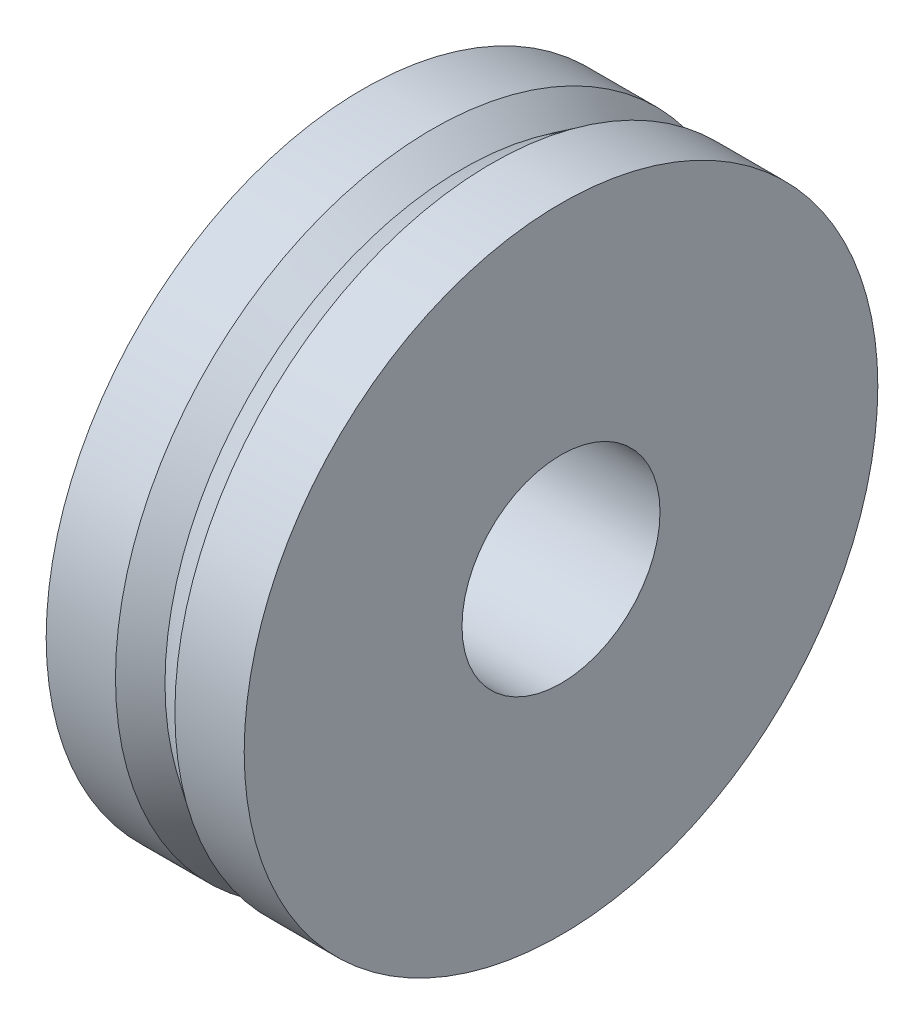
SolidWorks part; units mm, degrees
ref_plane "Front" through (0, 0, 0) normal (0, 0, 1) x (1, 0, 0)
ref_plane "Top" through (0, 0, 0) normal (0, 1, 0) x (1, 0, 0)
ref_plane "Right" through (0, 0, 0) normal (1, 0, 0) x (0, 0, -1)
sketch "Sketch1" plane through (0, 0, 0) normal (1, 0, 0) x (0, 0, -1)
  circle A0 centre (0, 0) radius 2.5
  circle A1 centre (0, 0) radius 8
  dimension "D1" = 5
  dimension "D2" = 16
extrude "Boss-Extrude1" add sketch "Sketch1" along normal blind 5
sketch "Sketch2" plane through (0, 0, 0) normal (0, 1, 0) x (1, 0, 0)
  line L0 (0, 0) -> (5, 0) construction
  line L1 (5, -8) -> (5, 8) construction
  line L2 (2.5, 0) -> (2.5, 8) construction
  line L3 (5, 8) -> (0, 8) construction
  line L4 (1.75, 8) -> (2.5, 7.5)
  line L5 (5, 8) -> (0, 8) construction
  line L6 (2.5, 7.5) -> (3.25, 8)
  line L7 (5, 8) -> (0, 8) construction
  line L8 (3.25, 8) -> (1.75, 8)
  dimension "D1" = 1.5
  dimension "D2" = 0.5
revolve "Cut-Revolve1" cut sketch "Sketch2" angle 360 about L0
